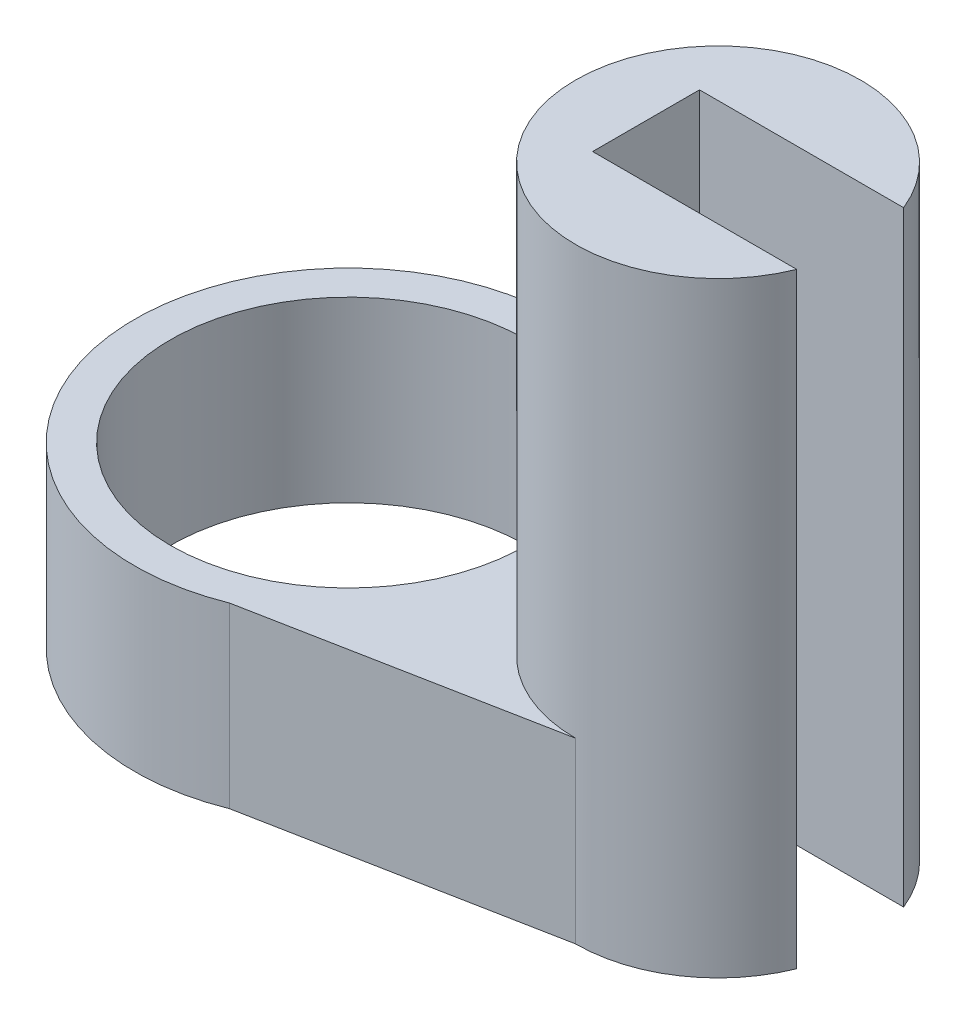
SolidWorks part; units mm, degrees
ref_plane "Front" through (0, 0, 0) normal (0, 0, 1) x (1, 0, 0)
ref_plane "Top" through (0, 0, 0) normal (0, 1, 0) x (1, 0, 0)
ref_plane "Right" through (0, 0, 0) normal (1, 0, 0) x (0, 0, -1)
sketch "草图1" plane through (0, 0, 0) normal (0, 1, 0) x (1, 0, 0)
  circle A0 centre (0, 0) radius 6
  dimension "D1" = 12
extrude "凸台-拉伸1" add sketch "草图1" along normal blind 5
sketch "草图3" plane through (0, 0, 0) normal (0, 1, 0) x (1, 0, 0)
  line L0 (17.6524, 0) -> (-11.8809, 0) construction
  circle A0 centre (10.3731, 0) radius 4
  dimension "D1" = 8
extrude "凸台-拉伸2" add sketch "草图3" along normal blind 5 separate body
sketch "草图4" plane through (0, 0, 0) normal (0, 1, 0) x (1, 0, 0)
  line L0 (0, 6) -> (10.3731, 4)
  line L1 (10.3731, 4) -> (10.3731, -4)
  line L2 (10.3731, -4) -> (0, -6)
  line L3 (0, -6) -> (0, 6)
  circle A0 centre (0, 0) radius 6 construction
  circle A1 centre (10.3731, 0) radius 4 construction
extrude "凸台-拉伸3" add sketch "草图4" along normal blind 5
sketch "草图2" plane through (0, 5, 0) normal (0, 1, 0) x (1, 0, 0)
  circle A0 centre (0, 0) radius 5
  dimension "D1" = 10
extrude "切除-拉伸1" cut sketch "草图2" against normal through all
sketch "草图5" plane through (0, 5, 0) normal (0, 1, 0) x (1, 0, 0)
  circle A0 centre (10.3731, 0) radius 4
  dimension "D1" = 8
extrude "凸台-拉伸4" add sketch "草图5" along normal blind 12
sketch "草图6" plane through (0, 17, 0) normal (0, 1, 0) x (1, 0, 0)
  line L0 (17.4745, 0) -> (-6.8053, 0) construction
  line L1 (10.3731, 0) -> (10.3731, 5.9241) construction
  line L6 (14.3519, 0) -> (14.3519, 5.9241) construction
  line L8 (18.9774, -1.5) -> (8.3519, -1.5)
  line L9 (18.9774, -1.5) -> (18.9774, 1.5)
  line L10 (18.9774, 1.5) -> (8.3519, 1.5)
  line L11 (8.3519, -1.5) -> (8.3519, 1.5)
  line L12 (18.9774, -1.5) -> (8.3519, 1.5) construction
  line L13 (18.9774, 1.5) -> (8.3519, -1.5) construction
  point P3 (14.4829, 0)
  point P9 (13.6647, 0)
  dimension "D1" = 3
  dimension "D2" = 6
extrude "切除-拉伸2" cut sketch "草图6" against normal through all
